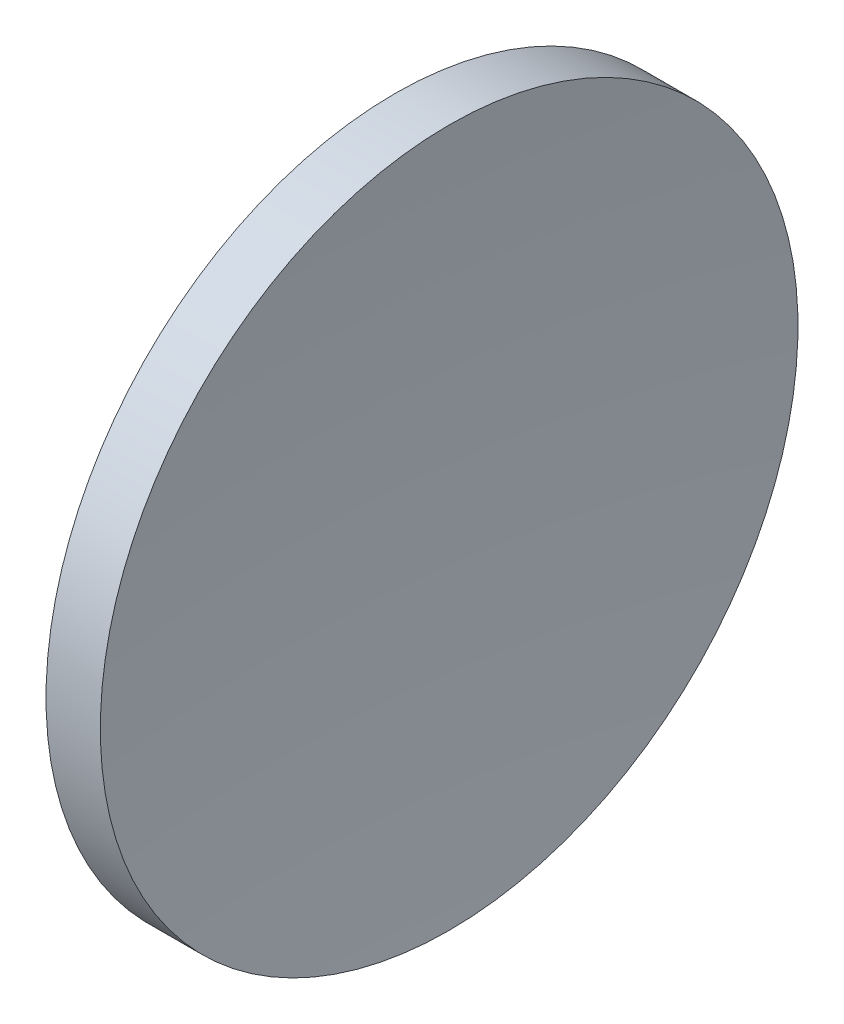
SolidWorks part; units mm, degrees
ref_plane "前视基准面" through (0, 0, 0) normal (0, 0, 1) x (1, 0, 0)
ref_plane "上视基准面" through (0, 0, 0) normal (0, 1, 0) x (1, 0, 0)
ref_plane "右视基准面" through (0, 0, 0) normal (1, 0, 0) x (0, 0, -1)
sketch "草图1" plane through (0, 0, 0) normal (0, 0, 1) x (1, 0, 0)
  line L0 (115.9445, 65.2168) -> (135.9482, 65.2168) construction
  line L1 (125.6133, 84.2418) -> (128.5751, 84.2418)
  line L2 (122.8554, 65.2168) -> (127.5554, 65.2168)
  arc A0 (125.6133, 84.2418) -> (122.8554, 65.2168) centre (189.8554, 65.2168) ccw
  arc A1 (128.5751, 84.2418) -> (127.5554, 65.2168) centre (305.5554, 65.2168) ccw
revolve "旋转1" add sketch "草图1" angle 360 about L0
